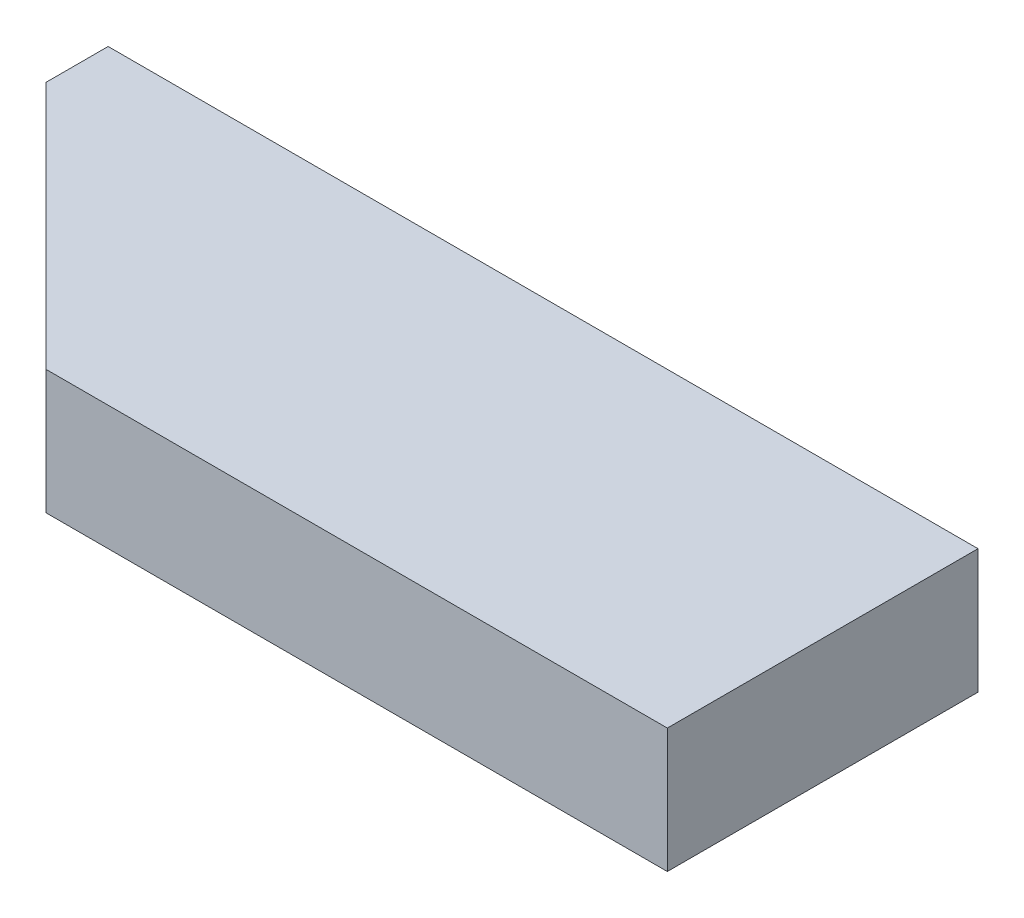
SolidWorks part; units mm, degrees
ref_plane "Front Plane" through (0, 0, 0) normal (0, 0, 1) x (1, 0, 0)
ref_plane "Top Plane" through (0, 0, 0) normal (0, 1, 0) x (1, 0, 0)
ref_plane "Right Plane" through (0, 0, 0) normal (1, 0, 0) x (0, 0, -1)
sketch "Sketch2" plane through (0, 0, 0) normal (0, 1, 0) x (1, 0, 0)
  line L1 (-35, 12.5) -> (35, 12.5)
  line L2 (-35, 12.5) -> (-35, -12.5)
  line L3 (-35, -12.5) -> (35, -12.5)
  line L4 (35, 12.5) -> (35, -12.5)
  line L5 (-35, 12.5) -> (35, -12.5) construction
  line L6 (-35, -12.5) -> (35, 12.5) construction
  point P0 (0, 0)
  dimension "D1" = 70
  dimension "D2" = 25
extrude "Boss-Extrude1" add sketch "Sketch2" along normal blind 10
sketch "Sketch3" plane through (0, 10, 0) normal (0, 1, 0) x (1, 0, 0)
  circle A0 centre (0, 0) radius 7.5
  dimension "D1" = 15
extrude "Cut-Extrude1" [suppressed] cut sketch "Sketch3" against normal blind 2.5
chamfer "Chamfer1" [suppressed] distance 0.5 angle 45
chamfer "Chamfer2" distance 20 angle 45 1 edges at (-35, 5, 12.5)
